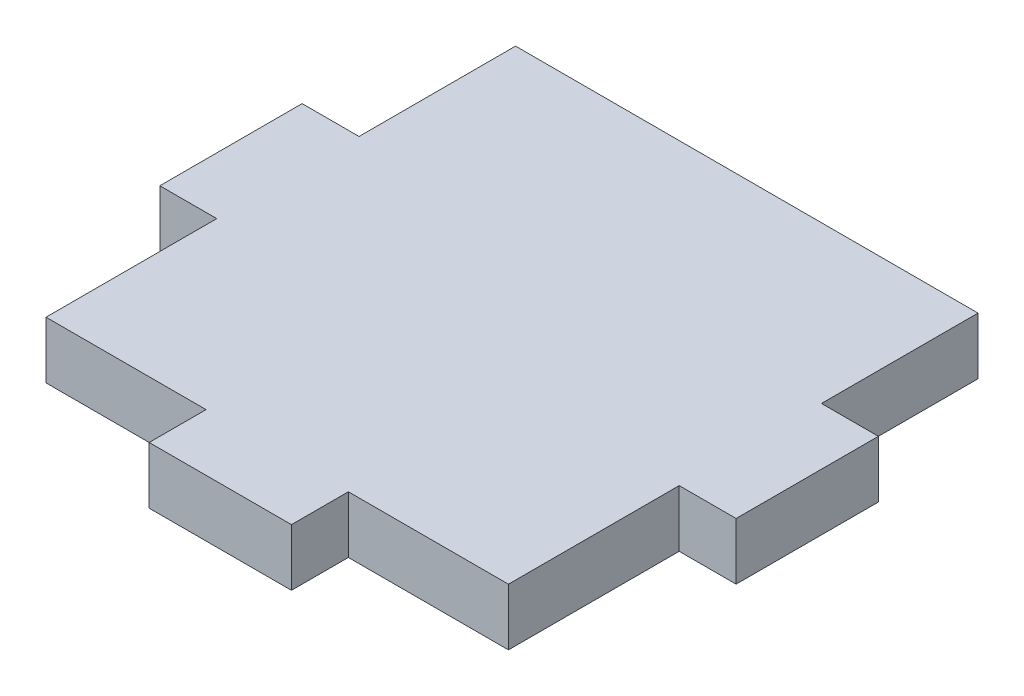
SolidWorks part; units mm, degrees
material "Maple"
ref_plane "Front Plane" through (0, 0, 0) normal (0, 0, 1) x (1, 0, 0)
ref_plane "Top Plane" through (0, 0, 0) normal (0, 1, 0) x (1, 0, 0)
ref_plane "Right Plane" through (0, 0, 0) normal (1, 0, 0) x (0, 0, -1)
sketch "Sketch1" plane through (0, 0, 0) normal (0, 1, 0) x (1, 0, 0)
  line L1 (0, 0) -> (32.5, 0)
  line L2 (0, 0) -> (0, -33)
  line L3 (0, -33) -> (32.5, -33)
  line L4 (32.5, 0) -> (32.5, -33)
  dimension "D1" = 32.5
  dimension "D2" = 33
extrude "Boss-Extrude1" add sketch "Sketch1" along normal blind 4
sketch "Sketch2" plane through (0, 0, 0) normal (0, -1, 0) x (1, 0, 0)
  line L0 (16.25, 33) -> (16.25, 0) construction
  line L1 (0, 33) -> (32.5, 33) construction
  line L2 (32.5, 0) -> (0, 0) construction
  line L4 (0, 0) -> (0, 33) construction
  line L5 (32.5, 33) -> (32.5, 0) construction
  line L7 (11.25, 37) -> (21.25, 37)
  line L8 (11.25, 37) -> (11.25, 33)
  line L9 (11.25, 33) -> (21.25, 33)
  line L10 (21.25, 37) -> (21.25, 33)
  line L11 (11.25, 37) -> (21.25, 33) construction
  line L12 (11.25, 33) -> (21.25, 37) construction
  line L13 (32.5, 21) -> (36.5, 21)
  line L14 (32.5, 21) -> (32.5, 11)
  line L15 (32.5, 11) -> (36.5, 11)
  line L16 (36.5, 21) -> (36.5, 11)
  line L17 (32.5, 21) -> (36.5, 11) construction
  line L18 (32.5, 11) -> (36.5, 21) construction
  line L19 (-4, 21) -> (0, 21)
  line L20 (-4, 21) -> (-4, 11)
  line L21 (-4, 11) -> (0, 11)
  line L22 (0, 21) -> (0, 11)
  line L23 (-4, 21) -> (0, 11) construction
  line L24 (-4, 11) -> (0, 21) construction
  point P12 (16.25, 35)
  point P17 (34.5, 16)
  point P22 (-2, 16)
  dimension "D1" = 4
  dimension "D2" = 10
  dimension "D3" = 12
extrude "Boss-Extrude2" add sketch "Sketch2" against normal through all
